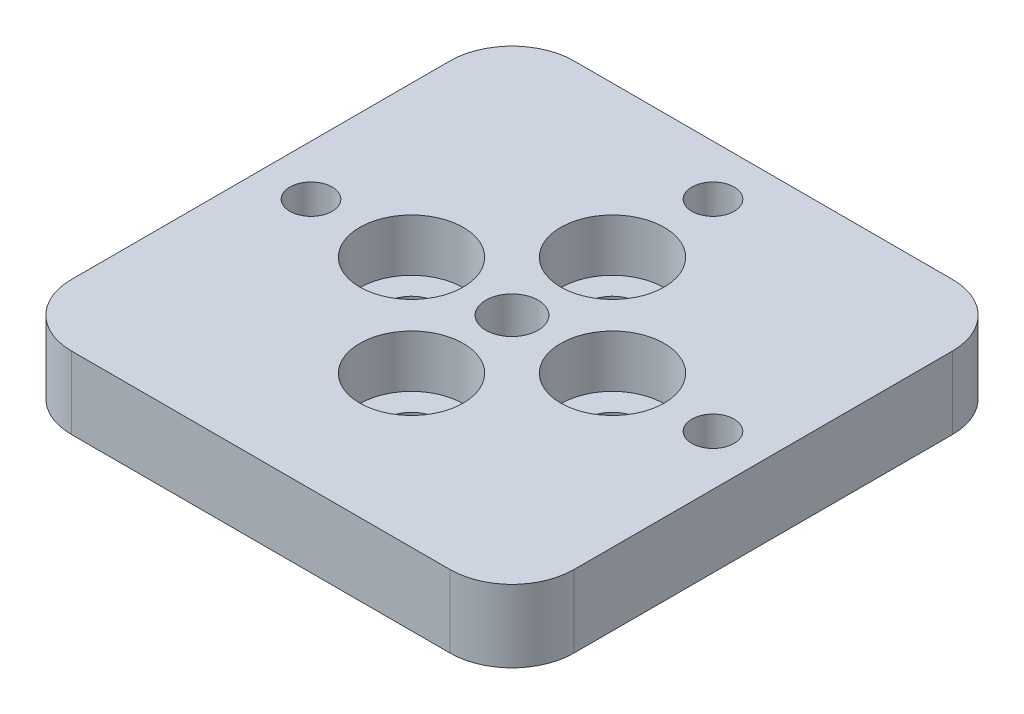
SolidWorks part; units mm, degrees
ref_plane "정면" through (0, 0, 0) normal (0, 0, 1) x (1, 0, 0)
ref_plane "윗면" through (0, 0, 0) normal (0, 1, 0) x (1, 0, 0)
ref_plane "우측면" through (0, 0, 0) normal (1, 0, 0) x (0, 0, -1)
sketch "스케치2" plane through (0, 0, 0) normal (0, 1, 0) x (1, 0, 0)
  line L1 (-25, 25) -> (25, 25)
  line L2 (-25, 25) -> (-25, -25)
  line L3 (-25, -25) -> (25, -25)
  line L4 (25, 25) -> (25, -25)
  line L5 (-25, 25) -> (25, -25) construction
  line L6 (-25, -25) -> (25, 25) construction
  circle A0 centre (0, 0) radius 2.6
  circle A1 centre (10, 0) radius 2.6
  circle A2 centre (0, -10) radius 2.6
  circle A3 centre (-10, 0) radius 2.6
  circle A4 centre (0, 10) radius 2.6
  point P4 (0, 0)
  point P10 (0, 0)
  point P11 (0, 0)
  point P12 (0, 0)
  point P19 (0, 0)
  dimension "D3" = 5.2
  dimension "D1" = 50
  dimension "D2" = 50
  dimension "D4" = 10
  dimension "D5" = 4
extrude "보스-돌출1" add sketch "스케치2" along normal blind 2
sketch "스케치3" plane through (0, 2, 0) normal (0, 1, 0) x (1, 0, 0)
  line L0 (25, -25) -> (25, 25) construction
  line L1 (-25, 25) -> (25, 25)
  line L2 (-25, 25) -> (-25, -25)
  line L3 (-25, -25) -> (25, -25)
  line L4 (25, 25) -> (25, -25)
  line L5 (-25, 25) -> (25, -25) construction
  line L6 (-25, -25) -> (25, 25) construction
  circle A0 centre (0, 0) radius 5.15 construction
  circle A1 centre (10, 0) radius 5.15
  circle A2 centre (10, 0) radius 2.6 construction
  circle A3 centre (0, -10) radius 5.15
  circle A4 centre (-10, 0) radius 5.15
  circle A5 centre (0, 10) radius 5.15
  circle A6 centre (-10, 0) radius 2.6 construction
  point P15 (0, 0)
  point P23 (0, 0)
  dimension "D1" = 10.3
  dimension "D2" = 4
extrude "보스-돌출2" add sketch "스케치3" along normal blind 5.2
sketch "스케치4" plane through (0, 7.2, 0) normal (0, 1, 0) x (1, 0, 0)
  line L0 (-25, -25) -> (25, -25) construction
  line L1 (-10, 10) -> (10, 10) construction
  line L2 (-10, 10) -> (-10, -25) construction
  line L3 (-10, -25) -> (10, -25) construction
  line L4 (10, 10) -> (10, -25) construction
  line L5 (-10, 10) -> (10, -25) construction
  line L6 (-10, -25) -> (10, 10) construction
  line L7 (0, 0) -> (20, 0) construction
  line L8 (0, 0) -> (0, 20) construction
  circle A2 centre (20, 0) radius 2.1
  circle A3 centre (0, 20) radius 2.1
  circle A4 centre (-20, 0) radius 2.1
  point P4 (0, -7.5)
  point P8 (0, -25)
  point P10 (0, 0)
  point P11 (0, 0)
  point P20 (0, 0)
  point P21 (0, 0)
  point P22 (0, 0)
  dimension "D4" = 4.2
  dimension "D1" = 20
  dimension "D2" = 10
  dimension "D3" = 20
  dimension "D6" = 90
  dimension "D5" = 3
extrude "컷-돌출1" cut sketch "스케치4" against normal blind 10
sketch "스케치6" plane through (0, 0, 0) normal (0, -1, 0) x (1, 0, 0)
  line L13 (-25, -25) -> (-25, 25) construction
  line L14 (-16.45, -2.0496) -> (-16.45, 2.0496)
  line L15 (-16.45, 2.0496) -> (-20, 4.0992)
  line L16 (-20, 4.0992) -> (-23.55, 2.0496)
  line L17 (-23.55, 2.0496) -> (-23.55, -2.0496)
  line L18 (-23.55, -2.0496) -> (-20, -4.0992)
  line L19 (-20, -4.0992) -> (-16.45, -2.0496)
  line L20 (2.0496, -16.45) -> (-2.0496, -16.45)
  line L21 (-2.0496, -16.45) -> (-4.0992, -20)
  line L22 (-4.0992, -20) -> (-2.0496, -23.55)
  line L23 (-2.0496, -23.55) -> (2.0496, -23.55)
  line L24 (2.0496, -23.55) -> (4.0992, -20)
  line L25 (4.0992, -20) -> (2.0496, -16.45)
  line L26 (16.45, 2.0496) -> (16.45, -2.0496)
  line L27 (16.45, -2.0496) -> (20, -4.0992)
  line L28 (20, -4.0992) -> (23.55, -2.0496)
  line L29 (23.55, -2.0496) -> (23.55, 2.0496)
  line L30 (23.55, 2.0496) -> (20, 4.0992)
  line L31 (20, 4.0992) -> (16.45, 2.0496)
  line L32 (0, 0) -> (-16.45, 2.0496) construction
  line L33 (0, 0) -> (-2.0496, -16.45) construction
  circle A0 centre (-20, 0) radius 3.55 construction
  circle A2 centre (0, -20) radius 3.55 construction
  circle A3 centre (20, 0) radius 3.55 construction
  dimension "D1" = 7.1
  dimension "D3" = 90
  dimension "D2" = 3
extrude "컷-돌출2" cut sketch "스케치6" against normal blind 3.5
fillet "필렛1" radius 6.17 1 edges at (25, 3.6, -25)
fillet "필렛2" radius 6.17 1 edges at (25, 3.6, 25)
fillet "필렛3" radius 6.17 1 edges at (-25, 3.6, 25)
fillet "필렛4" radius 6.17 1 edges at (-25, 3.6, -25)
